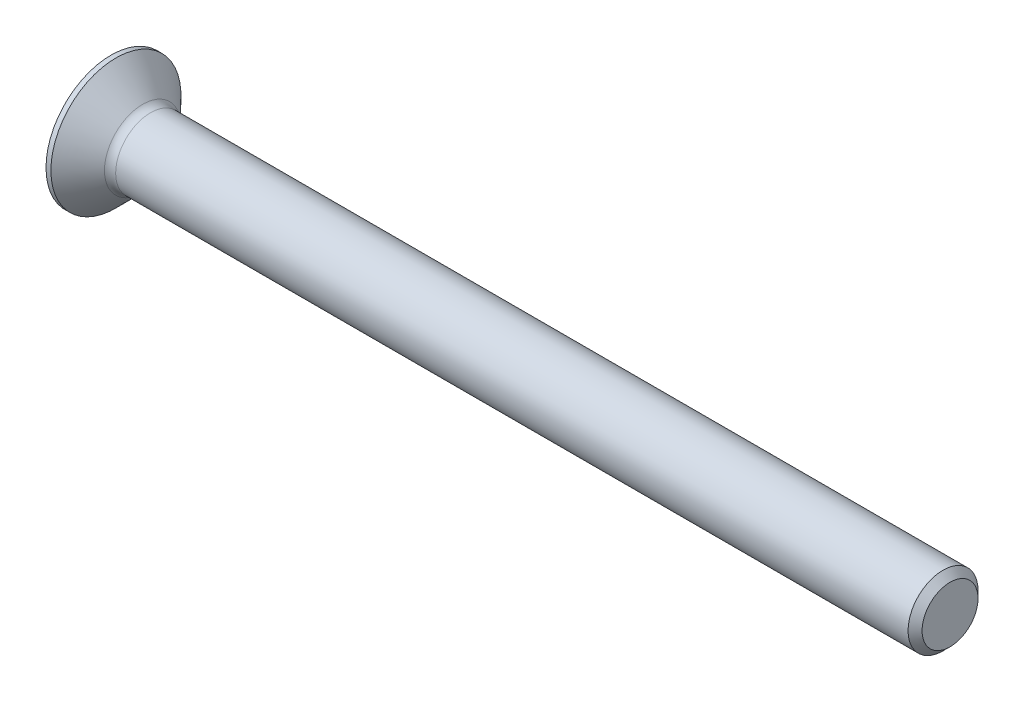
SolidWorks part; units mm, degrees
ref_plane "Plane1" through (0, 0, 0) normal (0, 0, 1) x (1, 0, 0)
ref_plane "Plane2" through (0, 0, 0) normal (0, 1, 0) x (1, 0, 0)
ref_plane "Plane3" through (0, 0, 0) normal (1, 0, 0) x (0, 0, -1)
sketch "BodySke" plane through (0, 0, 0) normal (0, 0, 1) x (1, 0, 0)
  line L0 (0, 0) -> (0, 4.65)
  line L1 (0, 4.65) -> (0.35, 4.65)
  line L2 (2.5, 2.5) -> (60, 2.5)
  line L3 (60, 2.5) -> (60, 0)
  line L4 (60, 0) -> (0, 0)
  line L5 (-6.35, 0) -> (82.55, 0) construction
  line L6 (2.5, -2.5) -> (60, -2.5) construction
  line L7 (0.35, -4.65) -> (2.5, -2.5) construction
  line L8 (0.35, 4.65) -> (2.5, 2.5)
  line L9 (0, -4.65) -> (0.35, -4.65) construction
  line L10 (3, 4.0875) -> (3, -5.4375) construction
  line L11 (0, 6.35) -> (0, -3.175) construction
  dimension "Diameter" = 5
  dimension "Length" = 60
  dimension "Head_ht" = 2.5
  dimension "Head_dia" = 9.3
  dimension "Head_ang" = 90
  dimension "D6" = 0.35
  dimension "Advance" = 0.5
revolve "Base-Revolve" add sketch "BodySke" angle 360 about L5
fillet "Fillet1" radius 0.8 1 edges at (2.5, 0, 2.5)
sketch "Sketch3" plane through (0, 0, 0) normal (-1, 0, 0) x (0, 0, 1)
  line L0 (-0.5, 2.5) -> (0.5, 2.5)
  line L1 (0.5, 2.5) -> (0.5, -2.5)
  line L2 (0.5, -2.5) -> (-0.5, -2.5)
  line L3 (-0.5, -2.5) -> (-0.5, 2.5)
  dimension "D1" = 2.5
  dimension "Cross_dia" = 5
  dimension "D2" = 0.5
  dimension "Cross_width" = 1
ref_plane "Plane4" through (2.01, 0, 0) normal (-1, 0, 0) x (0, 0, 1)
sketch "Sketch4" plane through (2.01, 0, 0) normal (-1, 0, 0) x (0, 0, 1)
  line L0 (-0.5, 0.5) -> (0.24, 0.5)
  line L3 (0.24, 0.5) -> (0.24, -0.5)
  line L4 (0.24, -0.5) -> (-0.5, -0.5)
  line L5 (-0.5, -0.5) -> (-0.5, 0.5)
  dimension "D1" = 0.74
  dimension "D2" = 1
  dimension "D3" = 0.5
  dimension "D4" = 0.5
loft "Recess" cut profiles "Sketch3", "Sketch4"
pattern_circular "RecPat" count 2 every 90 about axis through (0, 0, 0) along (1, 0, 0) of "Recess"
sketch "RecCorSke" plane through (0, 0, 0) normal (0, 0, 1) x (1, 0, 0)
  line L0 (-3.175, 0) -> (15.875, 0) construction
  line L2 (0, 0) -> (0, 0.6966)
  line L3 (0, 0.6966) -> (2.01, 0.556)
  line L4 (2.01, 0.556) -> (2.1907, 0)
  line L5 (2.1907, 0) -> (0, 0)
  dimension "Diameter" = 1.112
  dimension "Depth" = 2.01
  dimension "Draft_angle" = 4
  dimension "Bottom_angle" = 18
revolve "RecessCore" cut sketch "RecCorSke" angle 360 about L0
sketch "ThdSchSke" plane through (0, 0, 0) normal (0, 0, 1) x (1, 0, 0)
  line L0 (39, -1.2195) -> (38.1034, -2.5)
  line L1 (39, -1.2195) -> (39.8966, -2.5)
  line L2 (39.8966, -2.5) -> (39.8966, -3.125)
  line L3 (-3.175, 0) -> (5.1513, 0) construction
  line L5 (39.8966, -3.125) -> (38.1034, -3.125)
  line L6 (38.1034, -3.125) -> (38.1034, -2.5)
  line L7 (0, 4.65) -> (0, -4.65) construction
  dimension "Thread_minor" = 2.439
  dimension "Diameter" = 5
  dimension "Start" = 39
  dimension "SideAngle" = 55
  dimension "VeeAngle" = 70
  dimension "Overcut" = 6.25
revolve "ThreadSchematic" [suppressed] cut sketch "ThdSchSke" angle 360 about L3
pattern_linear "ThdSchPat" [suppressed]
chamfer "Chanfrein1" distance 0.5 angle 45 1 edges at (60, 0, 2.5)
